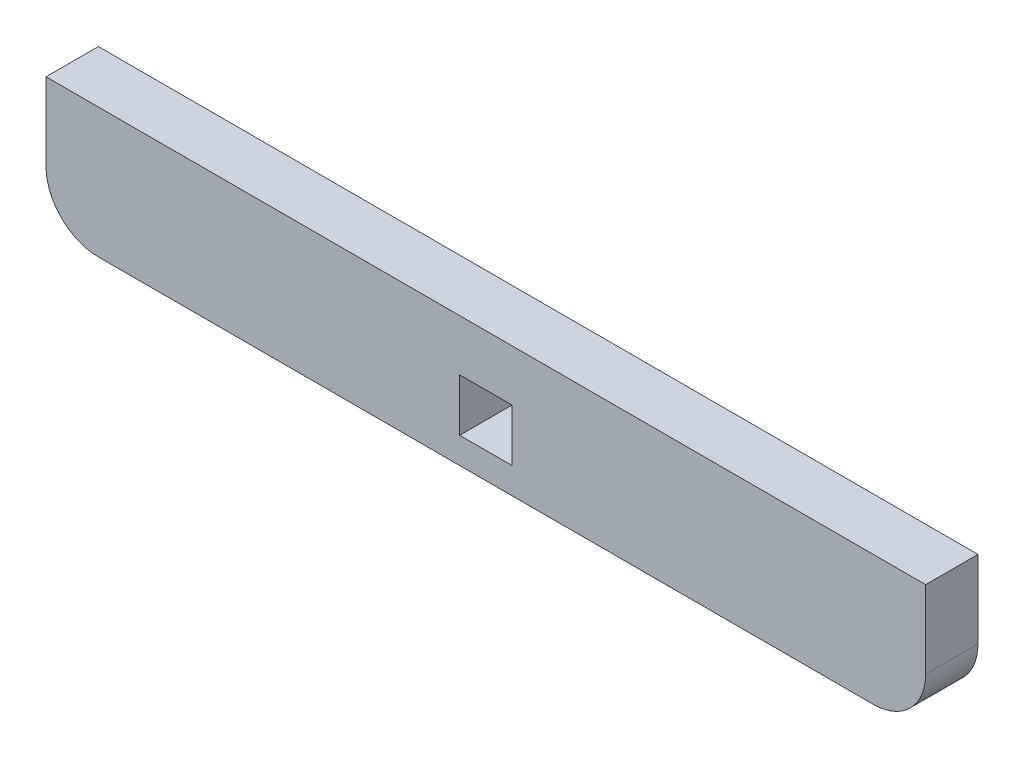
SolidWorks part; units mm, degrees
ref_plane "Front Plane" through (0, 0, 0) normal (0, 0, 1) x (1, 0, 0)
ref_plane "Top Plane" through (0, 0, 0) normal (0, 1, 0) x (1, 0, 0)
ref_plane "Right Plane" through (0, 0, 0) normal (1, 0, 0) x (0, 0, -1)
sketch "Sketch1" plane through (0, 0, 0) normal (0, 0, 1) x (1, 0, 0)
  line L0 (10.16, -2.286) -> (63.5, -2.286)
  line L1 (63.5, -6.985) -> (63.5, 4.6482) construction
  line L2 (63.5, -2.286) -> (63.5, -6.985)
  line L3 (60.325, -10.16) -> (13.335, -10.16)
  line L4 (10.16, -6.985) -> (10.16, -2.286)
  line L6 (3.175, -10.16) -> (60.325, -10.16) construction
  line L11 (35.2425, -5.3975) -> (35.2425, -8.5725)
  line L12 (35.2425, -8.5725) -> (38.4175, -8.5725)
  line L13 (38.4175, -8.5725) -> (38.4175, -5.3975)
  line L14 (38.4175, -5.3975) -> (35.2425, -5.3975)
  arc A0 (63.5, -6.985) -> (60.325, -10.16) centre (60.325, -6.985) cw
  arc A1 (13.335, -10.16) -> (10.16, -6.985) centre (13.335, -6.985) cw
  point P2 (38.4175, -6.985)
  point P15 (36.83, -8.5725)
  point P17 (36.83, -10.16)
  point P19 (36.5587, -5.3975)
  dimension "D2" = 3.175
  dimension "D1" = 7.874
  dimension "D3" = 53.34
  dimension "D4" = 3.175
  dimension "D5" = 3.175
  dimension "D6" = 1.5875
extrude "Boss-Extrude1" add sketch "Sketch1" along normal blind 3.175 contours L3 A1 L4 L0 L2 A0 | L11 L12 L13 L14
